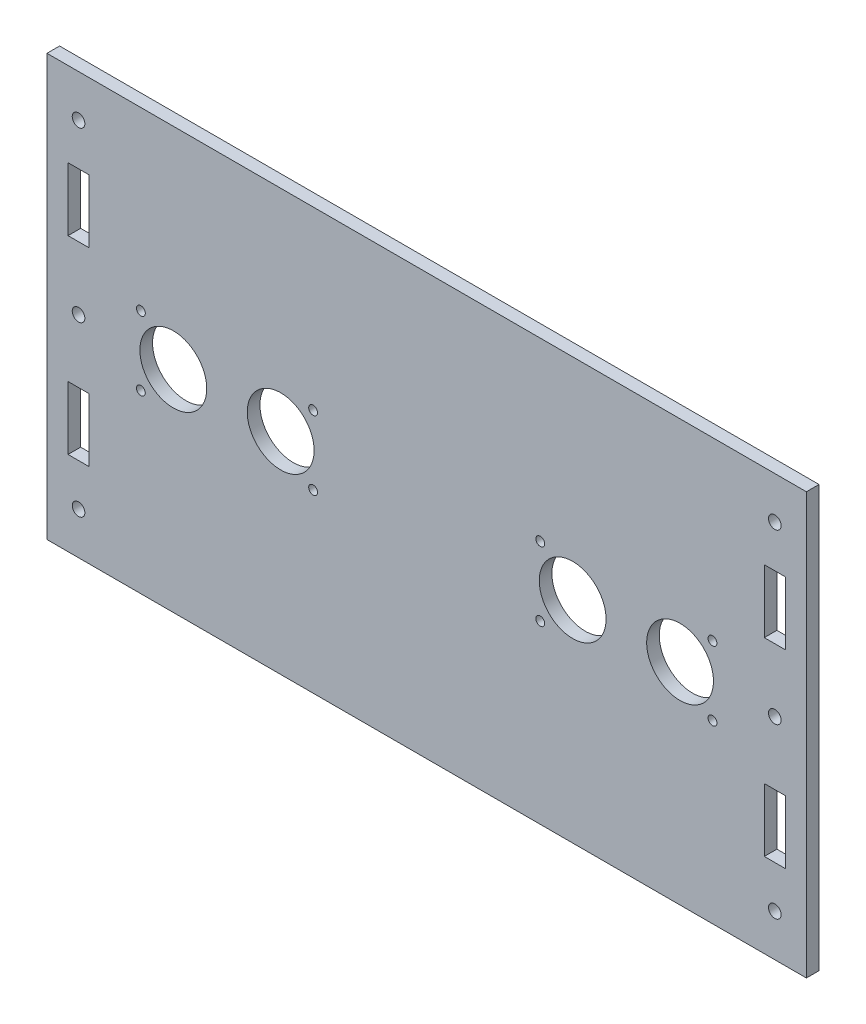
SolidWorks part; units mm, degrees
material "PMMA"
ref_plane "Front Plane" through (0, 0, 0) normal (0, 0, 1) x (1, 0, 0)
ref_plane "Top Plane" through (0, 0, 0) normal (0, 1, 0) x (1, 0, 0)
ref_plane "Right Plane" through (0, 0, 0) normal (1, 0, 0) x (0, 0, -1)
sketch "Schizzo1" plane through (0, 0, 0) normal (0, 0, 1) x (1, 0, 0)
  line L0 (90.17, 50) -> (-90.17, -50) construction
  line L1 (-90.17, 50) -> (90.17, 50)
  line L2 (-90.17, 50) -> (-90.17, -50)
  line L3 (-90.17, -50) -> (90.17, -50)
  line L4 (90.17, 50) -> (90.17, -50)
  point P4 (0, 0)
  dimension "D1" = 100
  dimension "D2" = 180.34
extrude "Estrusione-Estrusione1" add sketch "Schizzo1" along normal blind 3
sketch "Schizzo2" plane through (0, 0, 0) normal (0, 0, 1) x (1, 0, 0)
  line L0 (-90.17, 0) -> (90.17, 0) construction
  line L1 (-85.17, 30) -> (-80.17, 30)
  line L2 (-85.17, 30) -> (-85.17, 15)
  line L3 (-85.17, 15) -> (-80.17, 15)
  line L4 (-80.17, 30) -> (-80.17, 15)
  line L5 (-90.17, 50) -> (-90.17, -50) construction
  line L6 (90.17, -50) -> (90.17, 50) construction
  line L7 (0, 50) -> (0, -50) construction
  line L8 (90.17, 50) -> (-90.17, 50) construction
  line L9 (-90.17, -50) -> (90.17, -50) construction
  line L10 (-85.17, -30) -> (-85.17, -15)
  line L11 (-85.17, -15) -> (-80.17, -15)
  line L12 (-80.17, -30) -> (-80.17, -15)
  line L13 (-85.17, -30) -> (-80.17, -30)
  line L14 (85.17, 30) -> (85.17, 15)
  line L15 (85.17, 30) -> (80.17, 30)
  line L16 (80.17, 30) -> (80.17, 15)
  line L17 (85.17, 15) -> (80.17, 15)
  line L18 (85.17, -30) -> (85.17, -15)
  line L19 (85.17, -30) -> (80.17, -30)
  line L20 (80.17, -30) -> (80.17, -15)
  line L21 (85.17, -15) -> (80.17, -15)
  line L22 (-82.67, 15) -> (-82.67, -15) construction
  line L23 (-90.17, 40) -> (90.17, 40) construction
  circle A0 centre (-82.67, 0) radius 1.5
  circle A1 centre (82.67, 0) radius 1.5
  circle A2 centre (-82.67, 40) radius 1.5
  circle A3 centre (-82.67, -40) radius 1.5
  circle A4 centre (82.67, -40) radius 1.5
  circle A5 centre (82.67, 40) radius 1.5
  dimension "D5" = 3
  dimension "D1" = 5
  dimension "D2" = 5
  dimension "D3" = 15
  dimension "D4" = 15
  dimension "D6" = 40
extrude "Taglio-Estrusione1" cut sketch "Schizzo2" along direction (0, 0, 1) on the side of the normal through all
sketch "Schizzo3" plane through (0, 0, 0) normal (0, 0, 1) x (1, 0, 0)
  line L0 (-60.17, 0) -> (-34.67, 0) construction
  line L1 (-90.17, -50) -> (90.17, -50) construction
  line L2 (-90.17, 50) -> (-90.17, -50) construction
  line L3 (0, 50) -> (0, -50) construction
  line L4 (90.17, 50) -> (-90.17, 50) construction
  line L5 (-47.42, 0) -> (-47.42, 10.25) construction
  line L6 (-69.92, 10.25) -> (-24.92, 10.25) construction
  line L7 (-69.92, 10.25) -> (-69.92, -10.25) construction
  line L8 (-69.92, -10.25) -> (-24.92, -10.25) construction
  line L9 (-24.92, 10.25) -> (-24.92, -10.25) construction
  circle A0 centre (-60.17, 0) radius 7.94
  circle A1 centre (-34.67, 0) radius 7.94
  circle A2 centre (60.17, 0) radius 7.94
  circle A3 centre (34.67, 0) radius 7.94
  circle A4 centre (-26.97, -8.2) radius 1.05
  circle A5 centre (-26.97, 8.2) radius 1.05
  circle A6 centre (-67.87, -8.2) radius 1.05
  circle A7 centre (-67.87, 8.2) radius 1.05
  circle A8 centre (26.97, 8.2) radius 1.05
  circle A9 centre (26.97, -8.2) radius 1.05
  circle A10 centre (67.87, -8.2) radius 1.05
  circle A11 centre (67.87, 8.2) radius 1.05
  point P20 (-24.92, 0)
  point P23 (-47.42, 10.25)
  dimension "D2" = 15.88
  dimension "D5" = 45
  dimension "D7" = 2.1
  dimension "D1" = 25.5
  dimension "D3" = 50
  dimension "D4" = 30
  dimension "D6" = 20.5
  dimension "D8" = 2.05
  dimension "D9" = 2.05
extrude "Taglio-Estrusione2" cut sketch "Schizzo3" along direction (0, 0, 1) on the side of the normal through all
equation "\"Thickness3\"= 3"
equation "\"D1@Estrusione-Estrusione1\"=\"Thickness3\""
equation "\"Thickness5\"= 5"
equation "\"D1@Schizzo2\"=\"Thickness5\""
equation "\"D2@Schizzo2\"=\"Thickness5\""
